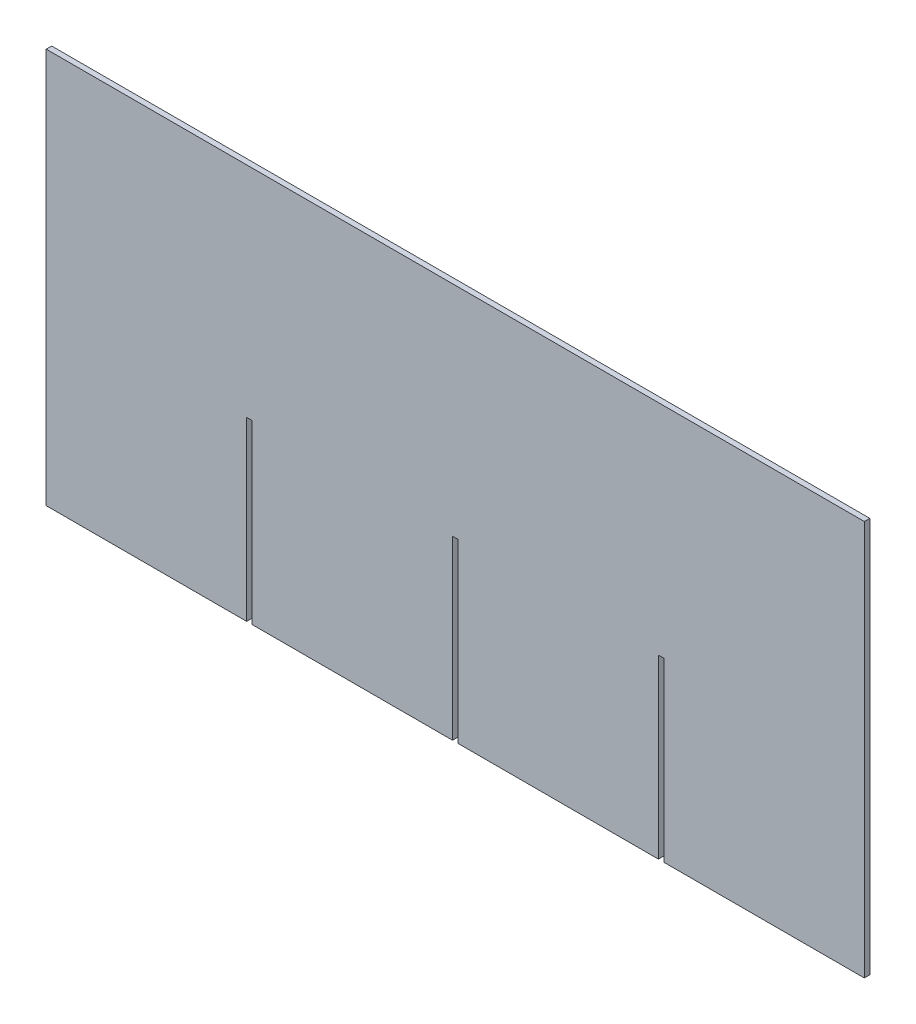
SolidWorks part; units mm, degrees
ref_plane "Front Plane" through (0, 0, 0) normal (0, 0, 1) x (1, 0, 0)
ref_plane "Top Plane" through (0, 0, 0) normal (0, 1, 0) x (1, 0, 0)
ref_plane "Right Plane" through (0, 0, 0) normal (1, 0, 0) x (0, 0, -1)
sketch "Sketch1" plane through (0, 0, 0) normal (0, 0, 1) x (1, 0, 0)
  line L0 (-113, 108.6585) -> (336, 108.6585)
  line L1 (336, 108.6585) -> (336, -108.3415)
  line L2 (336, -108.3415) -> (226, -108.3415)
  line L3 (226, -108.3415) -> (226, -11.3415)
  line L4 (226, -11.3415) -> (223, -11.3415)
  line L5 (223, -11.3415) -> (223, -108.3415)
  line L6 (223, -108.3415) -> (113, -108.3415)
  line L7 (113, -108.3415) -> (113, -11.3415)
  line L8 (113, -11.3415) -> (110, -11.3415)
  line L9 (110, -11.3415) -> (110, -108.3415)
  line L10 (110, -108.3415) -> (0, -108.3415)
  line L11 (0, -108.3415) -> (0, -11.3415)
  line L12 (0, -11.3415) -> (-3, -11.3415)
  line L13 (-3, -11.3415) -> (-3, -108.3415)
  line L14 (-3, -108.3415) -> (-113, -108.3415)
  line L15 (-113, -108.3415) -> (-113, 108.6585)
  dimension "D1" = 217
  dimension "D2" = 97
  dimension "D3" = 110
  dimension "D4" = 3
extrude "Boss-Extrude1" add sketch "Sketch1" along normal blind 3
